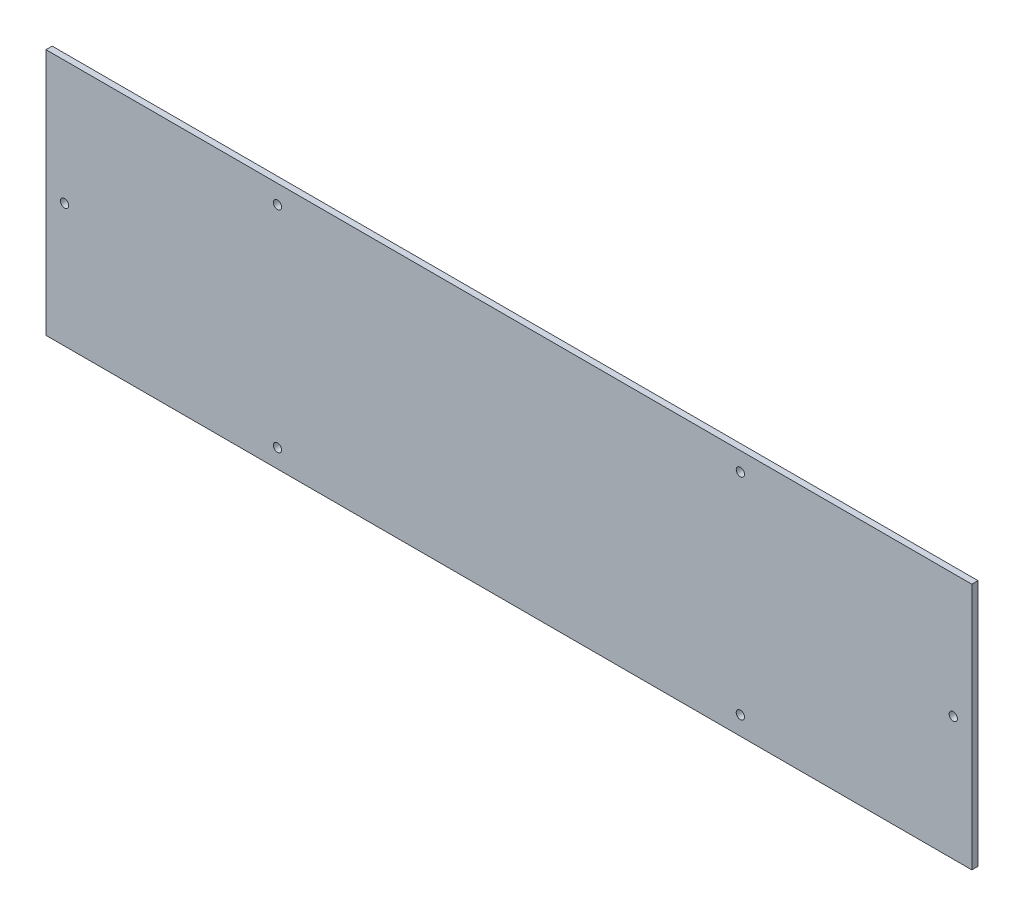
SolidWorks part; units mm, degrees
material "PMMA"
ref_plane "Piano frontale" through (0, 0, 0) normal (0, 0, 1) x (1, 0, 0)
ref_plane "Piano superiore" through (0, 0, 0) normal (0, 1, 0) x (1, 0, 0)
ref_plane "Piano destro" through (0, 0, 0) normal (1, 0, 0) x (0, 0, -1)
sketch "Schizzo1" plane through (0, 0, 0) normal (0, 0, 1) x (1, 0, 0)
  line L0 (0, 0) -> (0, 120)
  line L1 (0, 120) -> (449, 120)
  line L2 (449, 120) -> (449, 0)
  line L3 (449, 0) -> (0, 0)
  line L4 (0, 60) -> (449, 60) construction
  line L5 (224.5, 68) -> (224.5, 149.488) construction
  line L6 (224.5, 120) -> (0, 0) construction
  line L7 (112.25, 60) -> (112.25, 120) construction
  circle A0 centre (9, 60) radius 2
  circle A3 centre (440, 60) radius 2
  circle A9 centre (112.25, 111) radius 2
  circle A10 centre (336.75, 111) radius 2
  circle A11 centre (336.75, 9) radius 2
  circle A12 centre (112.25, 9) radius 2
  dimension "D3" = 9
  dimension "D6" = 4
  dimension "D7" = 4
  dimension "D1" = 120
  dimension "D2" = 449
  dimension "D8" = 9
extrude "Estrusione-Estrusione1" add sketch "Schizzo1" along normal blind 3
